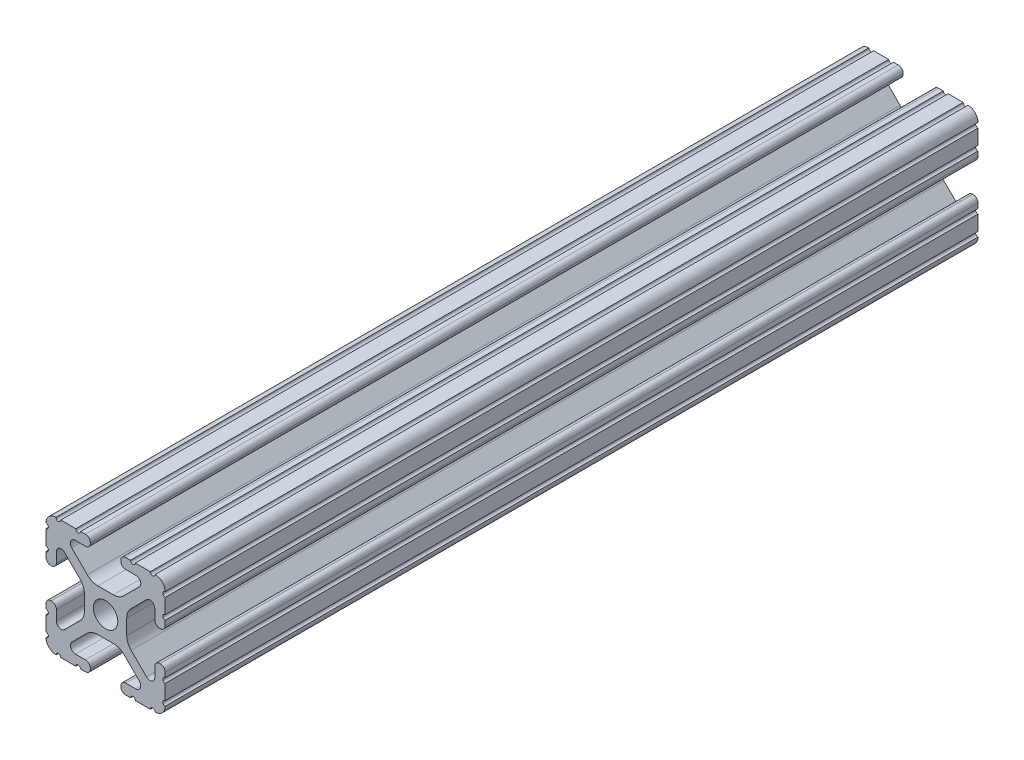
SolidWorks part; units mm, degrees
ref_plane "Front Plane" through (0, 0, 0) normal (0, 0, 1) x (1, 0, 0)
ref_plane "Top Plane" through (0, 0, 0) normal (0, 1, 0) x (1, 0, 0)
ref_plane "Right Plane" through (0, 0, 0) normal (1, 0, 0) x (0, 0, -1)
sketch "Sketch1" plane through (0, 0, 0) normal (0, 0, 1) x (1, 0, 0)
  line L88 (-7.1797, -8.6452) -> (-3.9523, -5.4237)
  line L89 (-1.7093, -4.4958) -> (1.7093, -4.4958)
  line L90 (3.9523, -5.4237) -> (7.1797, -8.6452)
  line L91 (6.4164, -10.4902) -> (4.2875, -10.4902)
  line L92 (3.2385, -11.5392) -> (3.2385, -11.651)
  line L93 (4.2875, -12.7) -> (5.3171, -12.7)
  line L94 (6.3331, -12.7) -> (9.5504, -12.7)
  line L95 (12.7, -9.5504) -> (12.7, -6.3331)
  line L96 (12.7, -5.3171) -> (12.7, -4.2875)
  line L97 (11.651, -3.2385) -> (11.5392, -3.2385)
  line L98 (10.4902, -4.2875) -> (10.4902, -6.4021)
  line L99 (8.7371, -7.1294) -> (5.441, -3.8408)
  line L100 (4.5085, -1.5932) -> (4.5085, 1.5932)
  line L101 (5.441, 3.8408) -> (8.7371, 7.1294)
  line L102 (10.4902, 6.4021) -> (10.4902, 4.2875)
  line L103 (11.5392, 3.2385) -> (11.651, 3.2385)
  line L104 (12.7, 4.2875) -> (12.7, 5.3171)
  line L105 (12.7, 6.3331) -> (12.7, 9.5504)
  line L106 (9.5504, 12.7) -> (6.3331, 12.7)
  line L107 (5.3171, 12.7) -> (4.2875, 12.7)
  line L108 (3.2385, 11.651) -> (3.2385, 11.5392)
  line L109 (4.2875, 10.4902) -> (6.4768, 10.4902)
  line L110 (7.207, 8.7244) -> (3.8983, 5.4232)
  line L111 (1.6558, 4.4958) -> (-1.6558, 4.4958)
  line L112 (-3.8983, 5.4232) -> (-7.207, 8.7244)
  line L113 (-6.4768, 10.4902) -> (-4.2875, 10.4902)
  line L114 (-3.2385, 11.5392) -> (-3.2385, 11.651)
  line L115 (-4.2875, 12.7) -> (-5.3171, 12.7)
  line L116 (-6.3331, 12.7) -> (-9.5504, 12.7)
  line L117 (-12.7, 9.5504) -> (-12.7, 6.3331)
  line L118 (-12.7, 5.3171) -> (-12.7, 4.2875)
  line L119 (-11.651, 3.2385) -> (-11.5392, 3.2385)
  line L120 (-10.4902, 4.2875) -> (-10.4902, 6.4021)
  line L121 (-8.7371, 7.1294) -> (-5.441, 3.8408)
  line L122 (-4.5085, 1.5932) -> (-4.5085, -1.5932)
  line L123 (-5.441, -3.8408) -> (-8.7371, -7.1294)
  line L124 (-10.4902, -6.4021) -> (-10.4902, -4.2875)
  line L125 (-11.5392, -3.2385) -> (-11.651, -3.2385)
  line L126 (-12.7, -4.2875) -> (-12.7, -5.3171)
  line L127 (-12.7, -6.3331) -> (-12.7, -9.5504)
  line L128 (-9.5504, -12.7) -> (-6.3331, -12.7)
  line L129 (-5.3171, -12.7) -> (-4.2875, -12.7)
  line L130 (-3.2385, -11.651) -> (-3.2385, -11.5392)
  line L131 (-4.2875, -10.4902) -> (-6.4164, -10.4902)
  circle A1 centre (0, 0) radius 2.6035
  arc A104 (-7.1797, -8.6452) -> (-6.4164, -10.4902) centre (-6.4164, -9.4098) ccw
  arc A105 (-1.7093, -4.4958) -> (-3.9523, -5.4237) centre (-1.7093, -7.6708) ccw
  arc A106 (3.9523, -5.4237) -> (1.7093, -4.4958) centre (1.7093, -7.6708) ccw
  arc A107 (6.4164, -10.4902) -> (7.1797, -8.6452) centre (6.4164, -9.4098) ccw
  arc A108 (4.2875, -10.4902) -> (3.2385, -11.5392) centre (4.2875, -11.5392) ccw
  arc A109 (3.2385, -11.651) -> (4.2875, -12.7) centre (4.2875, -11.651) ccw
  arc A110 (6.3331, -12.7) -> (5.3171, -12.7) centre (5.8251, -12.7) ccw
  arc A111 (10.5664, -12.6998) -> (9.5504, -12.7) centre (10.0584, -12.7) ccw
  arc A112 (10.5664, -12.6998) -> (12.6998, -10.5664) centre (10.5918, -10.5918) ccw
  arc A113 (12.7, -9.5504) -> (12.6998, -10.5664) centre (12.7, -10.0584) ccw
  arc A114 (12.7, -5.3171) -> (12.7, -6.3331) centre (12.7, -5.8251) ccw
  arc A115 (12.7, -4.2875) -> (11.651, -3.2385) centre (11.651, -4.2875) ccw
  arc A116 (11.5392, -3.2385) -> (10.4902, -4.2875) centre (11.5392, -4.2875) ccw
  arc A117 (8.7371, -7.1294) -> (10.4902, -6.4021) centre (9.4628, -6.4021) ccw
  arc A118 (4.5085, -1.5932) -> (5.441, -3.8408) centre (7.6835, -1.5932) ccw
  arc A119 (5.441, 3.8408) -> (4.5085, 1.5932) centre (7.6835, 1.5932) ccw
  arc A120 (10.4902, 6.4021) -> (8.7371, 7.1294) centre (9.4628, 6.4021) ccw
  arc A121 (10.4902, 4.2875) -> (11.5392, 3.2385) centre (11.5392, 4.2875) ccw
  arc A122 (11.651, 3.2385) -> (12.7, 4.2875) centre (11.651, 4.2875) ccw
  arc A123 (12.7, 6.3331) -> (12.7, 5.3171) centre (12.7, 5.8251) ccw
  arc A124 (12.6998, 10.5664) -> (12.7, 9.5504) centre (12.7, 10.0584) ccw
  arc A125 (12.6998, 10.5664) -> (10.5664, 12.6998) centre (10.5918, 10.5918) ccw
  arc A126 (9.5504, 12.7) -> (10.5664, 12.6998) centre (10.0584, 12.7) ccw
  arc A127 (5.3171, 12.7) -> (6.3331, 12.7) centre (5.8251, 12.7) ccw
  arc A128 (4.2875, 12.7) -> (3.2385, 11.651) centre (4.2875, 11.651) ccw
  arc A129 (3.2385, 11.5392) -> (4.2875, 10.4902) centre (4.2875, 11.5392) ccw
  arc A130 (7.207, 8.7244) -> (6.4768, 10.4902) centre (6.4768, 9.4563) ccw
  arc A131 (1.6558, 4.4958) -> (3.8983, 5.4232) centre (1.6558, 7.6708) ccw
  arc A132 (-3.8983, 5.4232) -> (-1.6558, 4.4958) centre (-1.6558, 7.6708) ccw
  arc A133 (-6.4768, 10.4902) -> (-7.207, 8.7244) centre (-6.4768, 9.4563) ccw
  arc A134 (-4.2875, 10.4902) -> (-3.2385, 11.5392) centre (-4.2875, 11.5392) ccw
  arc A135 (-3.2385, 11.651) -> (-4.2875, 12.7) centre (-4.2875, 11.651) ccw
  arc A136 (-6.3331, 12.7) -> (-5.3171, 12.7) centre (-5.8251, 12.7) ccw
  arc A137 (-10.5664, 12.6998) -> (-9.5504, 12.7) centre (-10.0584, 12.7) ccw
  arc A138 (-10.5664, 12.6998) -> (-12.6998, 10.5664) centre (-10.5918, 10.5918) ccw
  arc A139 (-12.7, 9.5504) -> (-12.6998, 10.5664) centre (-12.7, 10.0584) ccw
  arc A140 (-12.7, 5.3171) -> (-12.7, 6.3331) centre (-12.7, 5.8251) ccw
  arc A141 (-12.7, 4.2875) -> (-11.651, 3.2385) centre (-11.651, 4.2875) ccw
  arc A142 (-11.5392, 3.2385) -> (-10.4902, 4.2875) centre (-11.5392, 4.2875) ccw
  arc A143 (-8.7371, 7.1294) -> (-10.4902, 6.4021) centre (-9.4628, 6.4021) ccw
  arc A144 (-4.5085, 1.5932) -> (-5.441, 3.8408) centre (-7.6835, 1.5932) ccw
  arc A145 (-5.441, -3.8408) -> (-4.5085, -1.5932) centre (-7.6835, -1.5932) ccw
  arc A146 (-10.4902, -6.4021) -> (-8.7371, -7.1294) centre (-9.4628, -6.4021) ccw
  arc A147 (-10.4902, -4.2875) -> (-11.5392, -3.2385) centre (-11.5392, -4.2875) ccw
  arc A148 (-11.651, -3.2385) -> (-12.7, -4.2875) centre (-11.651, -4.2875) ccw
  arc A149 (-12.7, -6.3331) -> (-12.7, -5.3171) centre (-12.7, -5.8251) ccw
  arc A150 (-12.6998, -10.5664) -> (-12.7, -9.5504) centre (-12.7, -10.0584) ccw
  arc A151 (-12.6998, -10.5664) -> (-10.5664, -12.6998) centre (-10.5918, -10.5918) ccw
  arc A152 (-9.5504, -12.7) -> (-10.5664, -12.6998) centre (-10.0584, -12.7) ccw
  arc A153 (-5.3171, -12.7) -> (-6.3331, -12.7) centre (-5.8251, -12.7) ccw
  arc A154 (-4.2875, -12.7) -> (-3.2385, -11.651) centre (-4.2875, -11.651) ccw
  arc A155 (-3.2385, -11.5392) -> (-4.2875, -10.4902) centre (-4.2875, -11.5392) ccw
extrude "Boss-Extrude1" add sketch "Sketch1" along normal mid plane 173.2991
